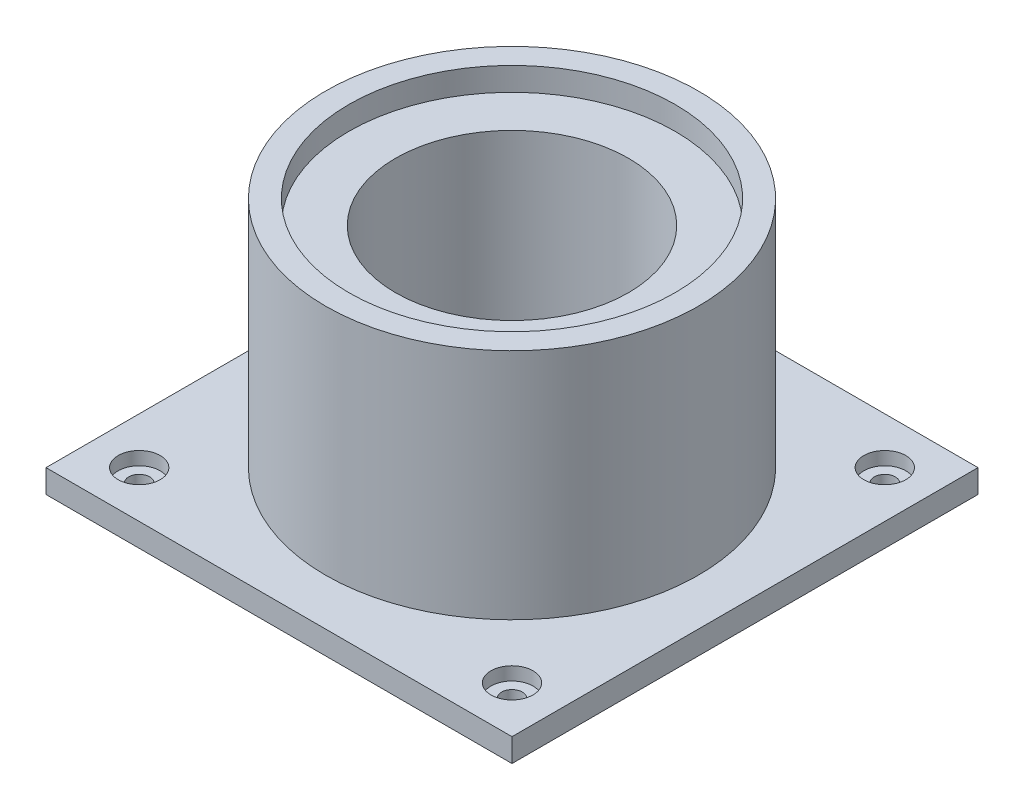
SolidWorks part; units mm, degrees
material "6063-T1"
ref_plane "Front Plane" through (0, 0, 0) normal (0, 0, 1) x (1, 0, 0)
ref_plane "Top Plane" through (0, 0, 0) normal (0, 1, 0) x (1, 0, 0)
ref_plane "Right Plane" through (0, 0, 0) normal (1, 0, 0) x (0, 0, -1)
sketch "Sketch1" plane through (0, 0, 0) normal (0, 1, 0) x (1, 0, 0)
  line L1 (100, -100) -> (-100, -100)
  line L2 (100, -100) -> (100, 100)
  line L3 (100, 100) -> (-100, 100)
  line L4 (-100, -100) -> (-100, 100)
  line L5 (100, -100) -> (-100, 100) construction
  line L6 (100, 100) -> (-100, -100) construction
  point P0 (0, 0)
  dimension "D1" = 200
  dimension "D2" = 200
extrude "Boss-Extrude1" add sketch "Sketch1" along normal blind 10
sketch "Sketch2" plane through (0, 10, 0) normal (0, 1, 0) x (1, 0, 0)
  circle A0 centre (0, 0) radius 80
  dimension "D1" = 160
extrude "Boss-Extrude2" add sketch "Sketch2" along normal blind 100
sketch "Sketch3" plane through (0, 110, 0) normal (0, 1, 0) x (1, 0, 0)
  circle A0 centre (0, 0) radius 50
  dimension "D1" = 100
extrude "Cut-Extrude1" cut sketch "Sketch3" against normal up to surface (100 mm away) up to face at (0, 10, 80)
sketch "Sketch4" plane through (0, 110, 0) normal (0, 1, 0) x (1, 0, 0)
  circle A0 centre (0, 0) radius 70
  dimension "D1" = 140
extrude "Cut-Extrude2" cut sketch "Sketch4" against normal blind 10
hole_wizard "CBORE for M8 Hex Head Bolt1" positions "3DSketch2" profile "Sketch6" counterbore size "M8" standard "ANSI Metric" end condition through all
sketch3d "3DSketch2"
  line L0 (100, 10, 100) -> (100, 10, -100) construction
  line L1 (100, 10, -100) -> (-100, 10, -100) construction
  line L2 (-100, 10, -100) -> (-100, 10, 100) construction
  line L3 (100, 10, 0) -> (-100, 10, 0) construction
  line L4 (-100, 10, 100) -> (100, 10, 100) construction
  point P0 (80, 10, -80)
  point P2 (-80, 10, -80)
  point P19 (80, 10, 80)
  point P21 (-80, 10, 80)
  dimension "D1" = 20
  dimension "D2" = 20
  dimension "D3" = 20
  dimension "D4" = 20
  dimension "D5" = 20
  dimension "D6" = 20
  dimension "D7" = 20
  dimension "D8" = 20
sketch "Sketch6" plane through (80, 10, -80) normal (1, 0, 0) x (0, 0, 1)
  line L0 (0, 0) -> (0, 10)
  line L1 (0, 10) -> (4.5, 10)
  line L3 (4.5, 10) -> (4.5, 5.68)
  line L4 (4.5, 5.68) -> (9.005, 5.68)
  line L5 (9.005, 5.68) -> (9.005, 0)
  line L7 (9.005, 0) -> (0, 0)
  line L11 (0, -6.35) -> (0, 107.95) construction
  dimension "Thru Hole Dia." = 9
  dimension "Thru Hole Depth" = 10
  dimension "C'Bore Dia." = 18.01
  dimension "C'Bore Depth" = 5.68
